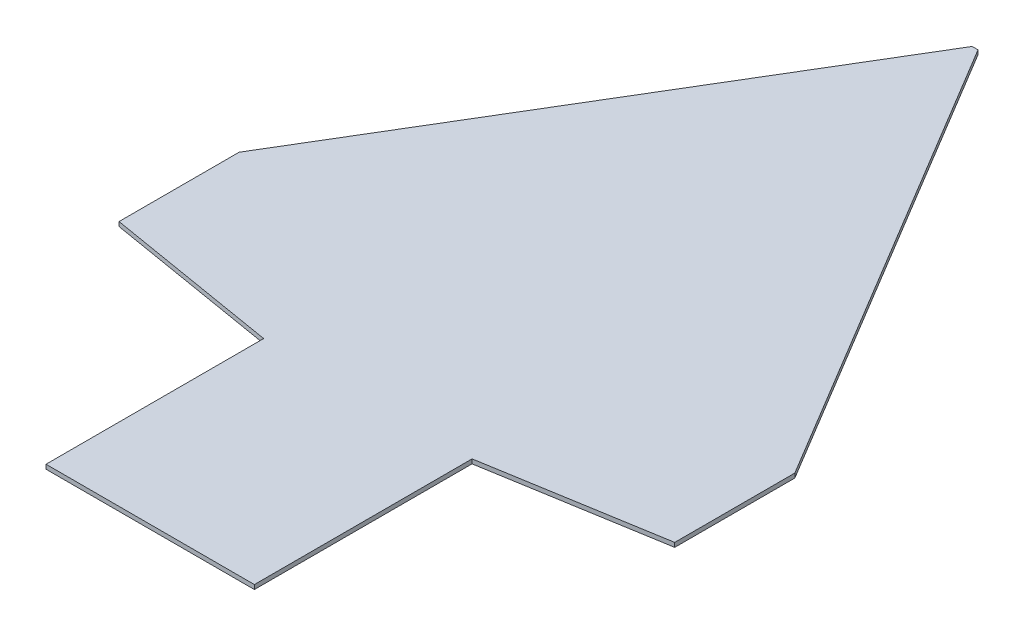
SolidWorks part; units mm, degrees
ref_plane "Front Plane" through (0, 0, 0) normal (0, 0, 1) x (1, 0, 0)
ref_plane "Top Plane" through (0, 0, 0) normal (0, 1, 0) x (1, 0, 0)
ref_plane "Right Plane" through (0, 0, 0) normal (1, 0, 0) x (0, 0, -1)
sketch "Sketch1" plane through (0, 0, 0) normal (0, 1, 0) x (1, 0, 0)
  line L6 (23.417, 69.5136) -> (23.417, -298.7864) construction
  line L7 (-215.343, -164.6932) -> (-215.343, -171.73)
  line L18 (25.131, 82.2136) -> (21.7029, 82.2136)
  line L23 (-215.343, -164.6932) -> (-215.343, -294.8391) construction
  line L24 (-37.543, -273.0345) -> (-37.543, -400.3864)
  line L26 (-189.943, -171.73) -> (-215.343, -171.73)
  line L27 (-37.543, -400.3864) -> (84.377, -400.3864)
  line L28 (84.377, -400.3864) -> (84.377, -273.0345)
  line L30 (262.177, -294.8391) -> (88.5617, -323.8393) construction
  line L31 (-215.343, -294.8391) -> (-41.7278, -323.8393) construction
  line L32 (-62.943, 89.2504) -> (-62.943, 209.2136) construction
  line L33 (-62.943, 209.2136) -> (251.5885, 209.2136) construction
  line L34 (-62.943, 89.2504) -> (-215.343, -164.6932) construction
  line L35 (251.5885, 209.2136) -> (251.5885, 56.8136) construction
  line L36 (251.5885, 56.8136) -> (129.2433, 56.8136) construction
  line L37 (129.2433, 56.8136) -> (262.177, -164.6932) construction
  line L38 (262.177, -164.6932) -> (262.177, -294.8391) construction
  line L43 (226.1885, 82.2136) -> (84.377, 82.2136) construction
  line L51 (-37.543, 183.8136) -> (226.1885, 183.8136) construction
  line L52 (-37.543, 82.2136) -> (-37.543, 183.8136) construction
  line L75 (-189.943, -273.33) -> (-37.543, -298.7864) construction
  line L77 (236.777, -273.33) -> (84.377, -298.7864) construction
  line L81 (39.9425, 82.2136) -> (6.8914, 82.2136) construction
  line L85 (-37.543, 82.2136) -> (-189.943, -171.73) construction
  line L87 (84.377, 82.2136) -> (236.777, -171.73) construction
  line L91 (-189.943, -171.73) -> (-189.943, -273.33) construction
  line L93 (236.777, -171.73) -> (236.777, -273.33) construction
  line L120 (21.7029, 82.2136) -> (-139.143, -185.8034)
  line L122 (-139.143, -185.8034) -> (-139.143, -256.0635)
  line L126 (226.1885, 183.8136) -> (226.1885, 82.2136) construction
  line L130 (185.977, -185.8034) -> (185.977, -256.0635)
  line L131 (25.131, 82.2136) -> (185.977, -185.8034)
  line L135 (185.977, -256.0635) -> (84.377, -273.0345)
  line L141 (-139.143, -256.0635) -> (-37.543, -273.0345)
  line L143 (14.0812, 69.5136) -> (-139.143, -185.8034) construction
  line L144 (32.7527, 69.5136) -> (185.977, -185.8034) construction
  line L145 (32.7527, 69.5136) -> (14.0812, 69.5136) construction
  line L146 (-139.143, -185.8034) -> (-139.143, -249.6255) construction
  line L147 (-37.543, -279.4724) -> (-37.543, -400.3864) construction
  line L148 (84.377, -400.3864) -> (84.377, -279.4724) construction
  line L149 (185.977, -185.8034) -> (185.977, -249.6255) construction
  line L150 (-145.493, -255.0028) -> (-31.193, -274.0951) construction
  line L151 (192.327, -255.0028) -> (78.027, -274.0951) construction
  line L176 (36.3476, 75.8636) -> (10.4863, 75.8636) construction
  line L177 (10.4863, 75.8636) -> (-145.493, -184.0443) construction
  line L178 (36.3476, 75.8636) -> (192.327, -184.0443) construction
  line L179 (-31.193, -274.0951) -> (-31.193, -394.0364) construction
  line L180 (-24.843, -268.7178) -> (-24.843, -387.6864) construction
  line L181 (71.677, -387.6864) -> (71.677, -268.7178) construction
  line L182 (78.027, -394.0364) -> (78.027, -274.0951) construction
  line L183 (-139.143, -249.6255) -> (-24.843, -268.7178) construction
  line L184 (185.977, -249.6255) -> (71.677, -268.7178) construction
  line L185 (-24.843, -387.6864) -> (71.677, -387.6864) construction
  line L186 (-31.193, -394.0364) -> (78.027, -394.0364) construction
  line L187 (-151.843, -260.3801) -> (-37.543, -279.4724) construction
  line L188 (198.677, -260.3801) -> (84.377, -279.4724) construction
  line L189 (39.9425, 82.2136) -> (198.677, -182.2851) construction
  line L190 (6.8914, 82.2136) -> (-151.843, -182.2851) construction
  line L191 (-145.493, -184.0443) -> (-145.493, -255.0028) construction
  line L192 (-151.843, -182.2851) -> (-151.843, -260.3801) construction
  line L193 (192.327, -184.0443) -> (192.327, -255.0028) construction
  line L194 (198.677, -182.2851) -> (198.677, -260.3801) construction
  dimension "D2" = 12.7
  dimension "D3" = 6.35
  dimension "D6" = 25.4
extrude "Boss-Extrude1" add sketch "Sketch1" along normal blind 2.54
